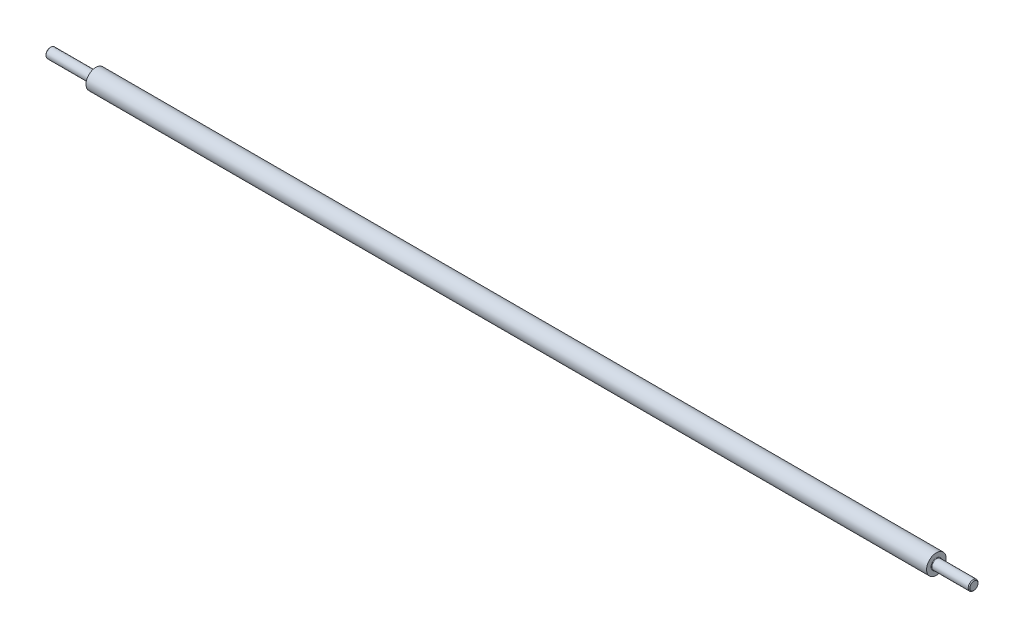
SolidWorks part; units mm, degrees
material "Plain Carbon Steel"
ref_plane "Front Plane" through (0, 0, 0) normal (0, 0, 1) x (1, 0, 0)
ref_plane "Top Plane" through (0, 0, 0) normal (0, 1, 0) x (1, 0, 0)
ref_plane "Right Plane" through (0, 0, 0) normal (1, 0, 0) x (0, 0, -1)
sketch "Sketch1" plane through (0, 0, 0) normal (0, 0, 1) x (1, 0, 0)
  line L0 (-24.9607, 51.57) -> (-678.441, 51.57) construction
  line L1 (-531.1, 51.57) -> (-581.1, 51.57) construction
  line L2 (-608.6, 54.57) -> (-636.6, 54.57)
  line L3 (-93.6, 57.57) -> (-608.6, 57.57)
  line L4 (-93.6, 57.57) -> (-93.6, 54.57)
  line L5 (-70.6, 51.57) -> (-636.6, 51.57)
  line L6 (-608.6, 57.57) -> (-608.6, 54.57)
  line L7 (-636.6, 54.57) -> (-636.6, 51.57)
  line L8 (-93.6, 54.57) -> (-70.6, 54.57)
  line L9 (-70.6, 54.57) -> (-70.6, 51.57)
  line L11 (-610.1, 174.68) -> (-610.1, 12.8) construction
  line L12 (-619.6, 54.57) -> (-619.6, 54.07) construction
  line L13 (-619.6, 54.07) -> (-636.6, 54.07) construction
  dimension "D1" = 12
  dimension "D2" = 6
  dimension "D3" = 6
  dimension "D4" = 1.5
  dimension "D5" = 515
  dimension "D6" = 23
  dimension "D7" = 28
  dimension "D8" = 5
  dimension "D9" = 17
  dimension "D10" = 566
revolve "Revolve1" add sketch "Sketch1" angle 360 about L0
cosmetic thread "Cosmetic Thread1" parameters "D2"=10
cosmetic thread "Cosmetic Thread2" parameters "D1"=15, "D2"=5.16
chamfer "Chamfer1" distance 0.5 angle 45 2 edges at (-70.6, 54.57, 0) (-636.6, 54.57, 0)
fillet "Fillet1" radius 0.3 2 edges at (-608.6, 54.57, 0) (-93.6, 54.57, 0)
